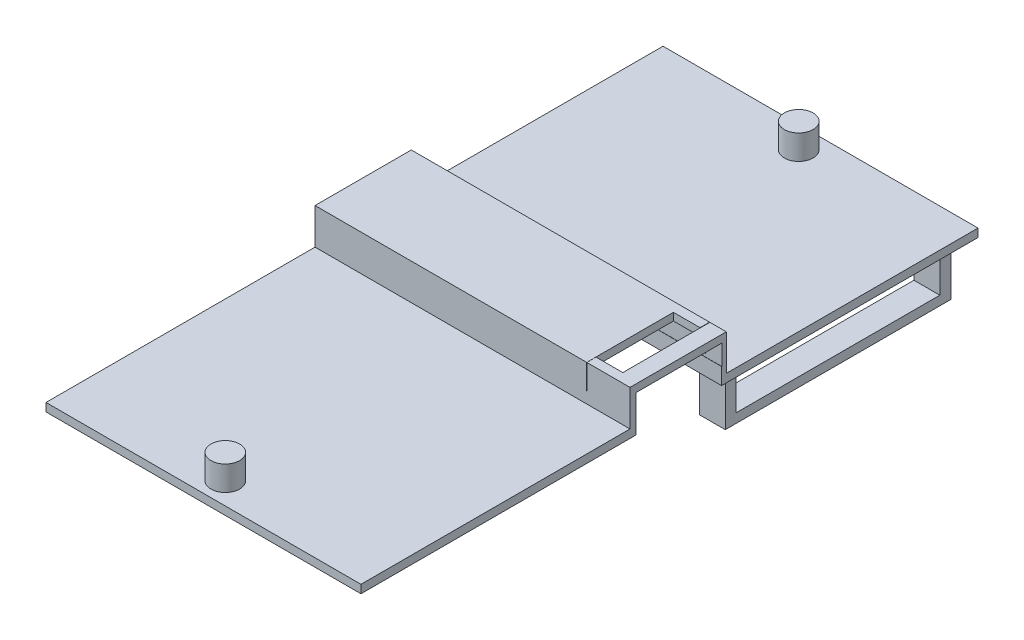
SolidWorks part; units mm, degrees
ref_plane "Alzado" through (0, 0, 0) normal (0, 0, 1) x (1, 0, 0)
ref_plane "Planta" through (0, 0, 0) normal (0, 1, 0) x (1, 0, 0)
ref_plane "Vista lateral" through (0, 0, 0) normal (1, 0, 0) x (0, 0, -1)
sketch "Croquis1" plane through (0, 0, 0) normal (0, 1, 0) x (1, 0, 0)
  line L1 (22.5, 37.5) -> (-22.5, 37.5)
  line L2 (22.5, 37.5) -> (22.5, -37.5)
  line L3 (22.5, -37.5) -> (-22.5, -37.5)
  line L4 (-22.5, 37.5) -> (-22.5, -37.5)
  line L5 (22.5, 37.5) -> (-22.5, -37.5) construction
  line L6 (22.5, -37.5) -> (-22.5, 37.5) construction
  point P0 (0, 0)
  dimension "D1" = 45
  dimension "D2" = 75
extrude "Saliente-Extruir1" add sketch "Croquis1" along normal blind 1
sketch "Croquis2" plane through (0, 1, 0) normal (0, 1, 0) x (1, 0, 0)
  line L0 (22.5, -37.5) -> (22.5, 37.5) construction
  line L1 (-22.5, -37.5) -> (22.5, -37.5)
  line L2 (-22.5, -37.5) -> (-22.5, -5.06)
  line L3 (-22.5, -5.06) -> (22.5, -5.06)
  line L4 (22.5, -37.5) -> (22.5, -5.06)
  line L5 (-22.5, 37.5) -> (-22.5, -37.5) construction
  line L6 (-22.5, 37.5) -> (22.5, 37.5)
  line L7 (-22.5, 37.5) -> (-22.5, 4.94)
  line L8 (-22.5, 4.94) -> (22.5, 4.94)
  line L9 (22.5, 37.5) -> (22.5, 4.94)
  line L10 (-22.5, 6.9) -> (22.5, 6.9)
  line L11 (-22.5, 6.9) -> (-22.5, -4.8)
  line L12 (-22.5, -4.8) -> (22.5, -4.8)
  line L13 (22.5, 6.9) -> (22.5, -4.8)
  dimension "D3" = 11.7
  dimension "D4" = 30.6
extrude "Saliente-Extruir2" add sketch "Croquis2" along normal blind 1.38 contours L11 L10 L13 L12
sketch "Croquis5" plane through (0, 0, 0) normal (0, -1, 0) x (1, 0, 0)
  line L0 (22.5, -37.5) -> (-22.5, -37.5) construction
  line L1 (22.5, 37.5) -> (15.7853, 37.5)
  line L2 (22.5, 37.5) -> (22.5, -37.5)
  line L3 (22.5, -37.5) -> (15.7853, -37.5)
  line L4 (15.7853, 37.5) -> (15.7853, -37.5)
extrude "Cortar-Extruir2" cut sketch "Croquis5" against normal blind 38.3
sketch "Croquis7" plane through (0, 1, 0) normal (0, 1, 0) x (1, 0, 0)
  line L1 (15.7853, 37.5) -> (-22.5, 37.5) construction
  line L2 (-22.5, -37.5) -> (15.7853, -37.5) construction
  circle A1 centre (-3.3574, 34.85) radius 1.75
  circle A2 centre (-3.3574, -34.85) radius 1.745
  dimension "D1" = 3.5
  dimension "D3" = 3.49
  dimension "D4" = 2.65
  dimension "D2" = 2.65
extrude "Saliente-Extruir3" add sketch "Croquis7" along normal blind 3
sketch "Croquis8" plane through (-22.5, 0, 0) normal (-1, 0, 0) x (0, 0, 1)
  line L0 (-37.5, 0) -> (37.5, 0) construction
  line L1 (-6.3306, 0) -> (4.0735, 0)
  line L2 (-6.3306, 0) -> (-6.3306, 2.0096)
  line L3 (-6.3306, 2.0096) -> (4.0735, 2.0096)
  line L4 (4.0735, 0) -> (4.0735, 2.0096)
extrude "Cortar-Extruir3" cut sketch "Croquis8" against normal blind 40
sketch "Croquis9" plane through (0, 2.0096, 0) normal (0, -1, 0) x (1, 0, 0)
  line L0 (15.7853, 4.0735) -> (15.7853, -6.3306) construction
  line L1 (13.7553, 3.6801) -> (10.5389, 3.6801)
  line L2 (13.7553, 3.6801) -> (13.7553, -5.741)
  line L3 (13.7553, -5.741) -> (10.5389, -5.741)
  line L4 (10.5389, 3.6801) -> (10.5389, -5.741)
  dimension "D1" = 2.03
extrude "Cortar-Extruir5" cut sketch "Croquis9" against normal blind 10 contours L2 L1 L4 L3
sketch "Croquis10" plane through (0, 0, 0) normal (0, -1, 0) x (1, 0, 0)
  line L1 (10.5057, -8.9135) -> (13.6531, -8.9135)
  line L2 (10.5057, -8.9135) -> (10.5057, -36.3716)
  line L3 (10.5057, -36.3716) -> (13.6531, -36.3716)
  line L4 (13.6531, -8.9135) -> (13.6531, -36.3716)
  line L5 (-20.968, -8.9135) -> (-17.9292, -8.9135)
  line L6 (-20.968, -8.9135) -> (-20.968, -36.3716)
  line L7 (-20.968, -36.3716) -> (-17.9292, -36.3716)
  line L8 (-17.9292, -8.9135) -> (-17.9292, -36.3716)
extrude "Saliente-Extruir4" add sketch "Croquis10" along normal blind 7
sketch "Croquis11" plane through (13.6531, 0, 0) normal (1, 0, 0) x (0, 0, -1)
  line L1 (10.2264, -1.1982) -> (34.9914, -1.1982)
  line L2 (10.2264, -1.1982) -> (10.2264, -5.8801)
  line L3 (10.2264, -5.8801) -> (34.9914, -5.8801)
  line L4 (34.9914, -1.1982) -> (34.9914, -5.8801)
extrude "Cortar-Extruir6" cut sketch "Croquis11" against normal blind 47
sketch "Croquis12" plane through (0, 2.38, 0) normal (0, 1, 0) x (1, 0, 0)
  line L0 (-22.5, -4.8) -> (15.7853, -4.8) construction
  line L1 (-22.5, 6.9) -> (10.5216, 6.9)
  line L2 (-22.5, 6.9) -> (-22.5, -4.8)
  line L3 (-22.5, -4.8) -> (10.5216, -4.8)
  line L4 (10.5216, 6.9) -> (10.5216, -4.8)
  line L6 (15.7853, 6.9) -> (13.7922, 6.9)
  line L7 (15.7853, 6.9) -> (15.7853, -4.8)
  line L8 (15.7853, -4.8) -> (13.7922, -4.8)
  line L9 (13.7922, 6.9) -> (13.7922, -4.8)
  line L10 (10.5389, -3.6801) -> (13.7922, -3.6801)
  line L11 (10.5389, -3.6801) -> (10.5389, -4.8)
  line L12 (10.5389, -4.8) -> (13.7922, -4.8)
  line L13 (13.7922, -3.6801) -> (13.7922, -4.8)
  line L14 (10.5216, 6.9) -> (13.7553, 6.9)
  line L15 (10.5216, 6.9) -> (10.5216, 5.741)
  line L16 (10.5216, 5.741) -> (13.7553, 5.741)
  line L17 (13.7553, 6.9) -> (13.7553, 5.741)
  line M1 (-22.5, -4.8) -> (15.7853, -4.8)
  line M2 (15.7853, -4.8) -> (15.7853, 6.9)
  line M3 (15.7853, 6.9) -> (-22.5, 6.9)
  line M4 (-22.5, 6.9) -> (-22.5, -4.8)
  line M5 (10.5389, 5.741) -> (13.7553, 5.741)
  line M7 (13.7553, -3.6801) -> (10.5389, -3.6801)
extrude "Saliente-Extruir5" add sketch "Croquis12" along normal blind 3 contours L4 M3 M4 M1 | L17 L4 L16 M3 M5 | L9 M3 M1 M2 | L11 L9 L10 M7 M1
sketch "Croquis13" plane through (15.7853, 0, 0) normal (1, 0, 0) x (0, 0, -1)
  line L0 (-4.0735, 2.0096) -> (6.3306, 2.0096) construction
  line L1 (-4.0656, 2.0096) -> (6.3533, 2.0096)
  line L2 (-4.0656, 2.0096) -> (-4.0656, 4.4629)
  line L3 (-4.0656, 4.4629) -> (6.3533, 4.4629)
  line L4 (6.3533, 2.0096) -> (6.3533, 4.4629)
extrude "Cortar-Extruir7" cut sketch "Croquis13" against normal blind 43
